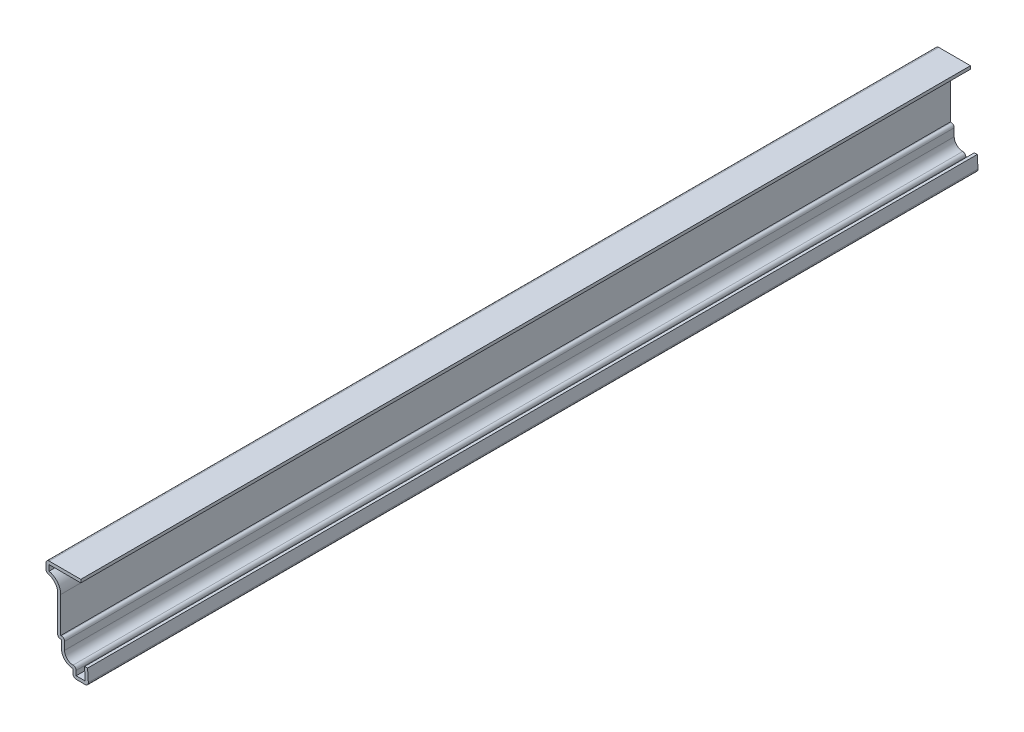
SolidWorks part; units mm, degrees
ref_plane "Front Plane" through (0, 0, 0) normal (0, 0, 1) x (1, 0, 0)
ref_plane "Top Plane" through (0, 0, 0) normal (0, 1, 0) x (1, 0, 0)
ref_plane "Right Plane" through (0, 0, 0) normal (1, 0, 0) x (0, 0, -1)
sketch "Sketch1" plane through (0, 0, 0) normal (0, 0, 1) x (1, 0, 0)
  line L0 (-0.3969, 6.35) -> (0, 0)
  line L1 (0, 0) -> (-6.35, 0)
  line L2 (-6.35, 0) -> (-6.35, 3.175)
  line L3 (-11.1125, 7.9375) -> (-11.1125, 11.1125)
  line L4 (-11.1125, 11.1125) -> (-12.7, 11.1125)
  line L5 (-12.7, 11.1125) -> (-12.7, 26.9875)
  line L6 (-17.4625, 31.75) -> (-17.4625, 36.5125)
  line L7 (-17.4625, 36.5125) -> (-3.175, 36.5125)
  arc A0 (-6.35, 3.175) -> (-11.1125, 7.9375) centre (-6.35, 7.9375) cw
  arc A1 (-12.7, 26.9875) -> (-17.4625, 31.75) centre (-17.4625, 26.9875) ccw
  point P12 (-6.4078, -2.6632)
  point P15 (-9.514, 4.0118)
  point P16 (-6.2095, 0)
  point P17 (-7.2233, 1.6355)
extrude "Extrude-Thin1" add sketch "Sketch1" against normal blind 365.125 thin
fillet "Fillet1" radius 1.27 7 edges at (0, 0, -182.5625) (-6.35, 0, -182.5625) (-5.08, 4.6841, -182.5625) (-9.8425, 12.3825, -182.5625) (-12.7, 11.1125, -182.5625) (-17.4625, 31.75, -182.5625) (-17.4625, 36.5125, -182.5625)
equation "\"D1@Extrude-Thin1\"=\"D13@Sketch1\"*10"
